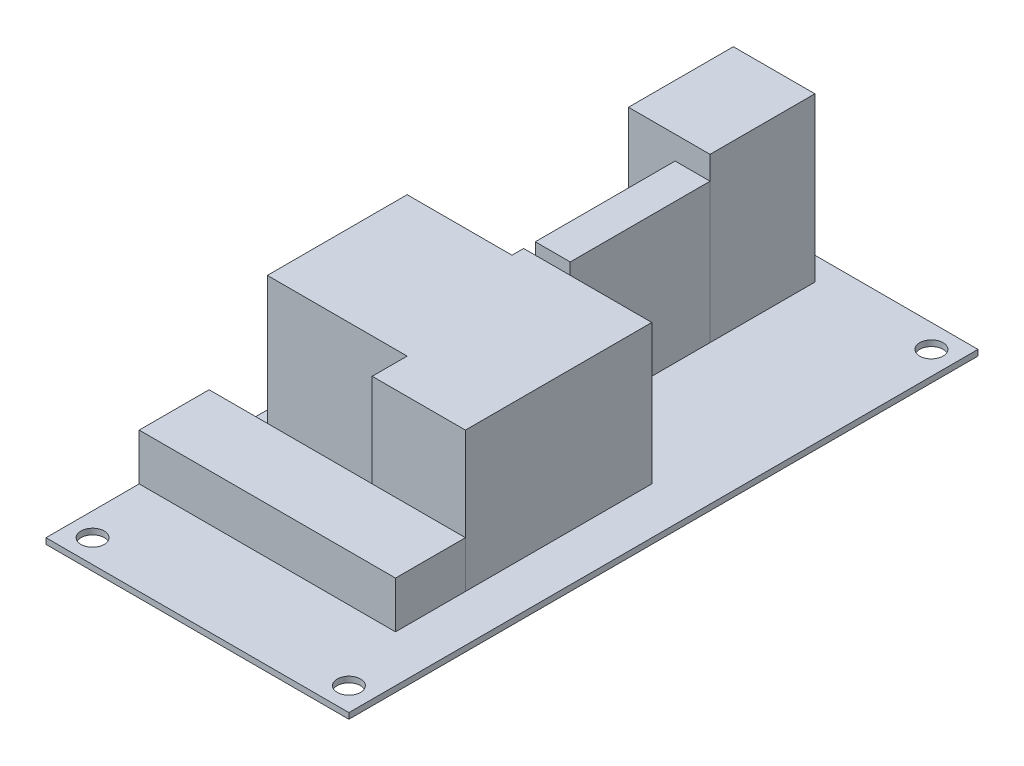
SolidWorks part; units mm, degrees
ref_plane "Front Plane" through (0, 0, 0) normal (0, 0, 1) x (1, 0, 0)
ref_plane "Top Plane" through (0, 0, 0) normal (0, 1, 0) x (1, 0, 0)
ref_plane "Right Plane" through (0, 0, 0) normal (1, 0, 0) x (0, 0, -1)
sketch "Sketch1" plane through (0, 0, 0) normal (0, 1, 0) x (1, 0, 0)
  line L1 (-20.6375, 42.8625) -> (20.6375, 42.8625)
  line L2 (-20.6375, 42.8625) -> (-20.6375, -42.8625)
  line L3 (-20.6375, -42.8625) -> (20.6375, -42.8625)
  line L4 (20.6375, 42.8625) -> (20.6375, -42.8625)
  line L5 (-20.6375, 42.8625) -> (20.6375, -42.8625) construction
  line L6 (-20.6375, -42.8625) -> (20.6375, 42.8625) construction
  point P0 (0, 0)
  dimension "D1" = 85.725
  dimension "D2" = 41.275
extrude "Boss-Extrude1" add sketch "Sketch1" along normal blind 0.7937
sketch "Sketch2" plane through (0, 0.7937, 0) normal (0, 1, 0) x (1, 0, 0)
  line L0 (-20.6375, 42.8625) -> (-20.6375, -42.8625) construction
  line L1 (-20.6375, -30.1625) -> (14.2875, -30.1625)
  line L2 (-20.6375, -30.1625) -> (-20.6375, -20.6375)
  line L3 (-20.6375, -20.6375) -> (14.2875, -20.6375)
  line L4 (14.2875, -30.1625) -> (14.2875, -20.6375)
  line L5 (-20.6375, -42.8625) -> (20.6375, -42.8625) construction
  dimension "D1" = 34.925
  dimension "D2" = 12.7
  dimension "D3" = 9.525
extrude "Boss-Extrude2" add sketch "Sketch2" along normal blind 6.35 separate body
sketch "Sketch3" plane through (0, 0.7937, 0) normal (0, 1, 0) x (1, 0, 0)
  line L0 (14.2875, -20.6375) -> (14.2875, 4.7625)
  line L1 (14.2875, 4.7625) -> (-3.175, 4.7625)
  line L2 (-3.175, 4.7625) -> (-3.175, 3.175)
  line L3 (-3.175, 3.175) -> (-17.4625, 3.175)
  line L4 (-17.4625, 3.175) -> (-17.4625, -15.875)
  line L5 (-17.4625, -15.875) -> (1.5875, -15.875)
  line L6 (1.5875, -15.875) -> (1.5875, -20.6375)
  line L8 (1.5875, -20.6375) -> (14.2875, -20.6375)
  line L9 (14.2875, -20.6375) -> (-20.6375, -20.6375) construction
  dimension "D1" = 17.4625
  dimension "D2" = 1.5875
  dimension "D3" = 14.2875
  dimension "D4" = 19.05
  dimension "D5" = 12.7
  dimension "D6" = 4.7625
extrude "Boss-Extrude3" add sketch "Sketch3" along normal blind 19.05 separate body
sketch "Sketch4" plane through (0, 0.7937, 0) normal (0, 1, 0) x (1, 0, 0)
  line L0 (-3.175, 4.7625) -> (-3.175, 3.175) construction
  line L1 (-14.2875, 9.525) -> (-3.175, 9.525)
  line L2 (-14.2875, 9.525) -> (-14.2875, 20.6375)
  line L3 (-14.2875, 20.6375) -> (-3.175, 20.6375)
  line L4 (-3.175, 9.525) -> (-3.175, 20.6375)
  line L6 (-3.175, 3.175) -> (-17.4625, 3.175) construction
  dimension "D1" = 6.35
  dimension "D2" = 11.1125
  dimension "D3" = 11.1125
extrude "Boss-Extrude4" add sketch "Sketch4" along normal blind 6.35 separate body
sketch "Sketch5" plane through (0, 7.1437, 0) normal (0, 1, 0) x (1, 0, 0)
  line L0 (-3.175, 20.6375) -> (-14.2875, 20.6375) construction
  line L1 (-14.2875, 20.6375) -> (-14.2875, 9.525) construction
  circle A0 centre (-8.7313, 15.0812) radius 2.3813
  point P5 (-8.7313, 20.6375)
  point P9 (-14.2875, 15.0812)
  dimension "D1" = 4.7625
extrude "Boss-Extrude5" add sketch "Sketch5" along normal blind 3.175 separate body
sketch "Sketch6" plane through (0, 0.7937, 0) normal (0, 1, 0) x (1, 0, 0)
  line L1 (-3.175, 6.35) -> (1.5875, 6.35)
  line L2 (-3.175, 6.35) -> (-3.175, 25.4)
  line L3 (-3.175, 25.4) -> (1.5875, 25.4)
  line L4 (1.5875, 6.35) -> (1.5875, 25.4)
  line L6 (-3.175, 9.525) -> (-3.175, 20.6375) construction
  line L7 (14.2875, 4.7625) -> (-3.175, 4.7625) construction
  dimension "D1" = 1.5875
  dimension "D2" = 4.7625
  dimension "D3" = 19.05
extrude "Boss-Extrude6" add sketch "Sketch6" along normal blind 19.05 separate body
sketch "Sketch7" plane through (0, 0.7937, 0) normal (0, 1, 0) x (1, 0, 0)
  line L0 (-20.6375, 42.8625) -> (-20.6375, -42.8625) construction
  line L1 (-9.525, 25.4) -> (1.5875, 25.4)
  line L2 (-9.525, 25.4) -> (-9.525, 39.6875)
  line L3 (-9.525, 39.6875) -> (1.5875, 39.6875)
  line L4 (1.5875, 25.4) -> (1.5875, 39.6875)
  line L5 (20.6375, 42.8625) -> (-20.6375, 42.8625) construction
  line L7 (1.5875, 6.35) -> (1.5875, 25.4) construction
  dimension "D1" = 11.1125
  dimension "D2" = 3.175
  dimension "D3" = 14.2875
extrude "Boss-Extrude7" add sketch "Sketch7" along normal blind 22.225 separate body
sketch "Sketch8" plane through (0, 0.7937, 0) normal (0, 1, 0) x (1, 0, 0)
  line L0 (-20.6375, 42.8625) -> (-20.6375, -42.8625) construction
  line L1 (-17.4625, -39.6875) -> (17.4625, -39.6875) construction
  line L2 (-17.4625, -39.6875) -> (-17.4625, 39.6875) construction
  line L3 (-17.4625, 39.6875) -> (17.4625, 39.6875) construction
  line L4 (17.4625, -39.6875) -> (17.4625, 39.6875) construction
  line L5 (20.6375, -42.8625) -> (20.6375, 42.8625) construction
  line L6 (20.6375, 42.8625) -> (-20.6375, 42.8625) construction
  line L7 (-20.6375, -42.8625) -> (20.6375, -42.8625) construction
  circle A3 centre (-17.4625, 39.6875) radius 1.5875
  circle A4 centre (17.4625, 39.6875) radius 1.5875
  circle A5 centre (-17.4625, -39.6875) radius 1.5875
  circle A6 centre (17.4625, -39.6875) radius 1.5875
  dimension "D5" = 3.175
  dimension "D1" = 3.175
  dimension "D2" = 3.175
  dimension "D3" = 3.175
  dimension "D4" = 3.175
extrude "Cut-Extrude1" cut sketch "Sketch8" against normal through all
